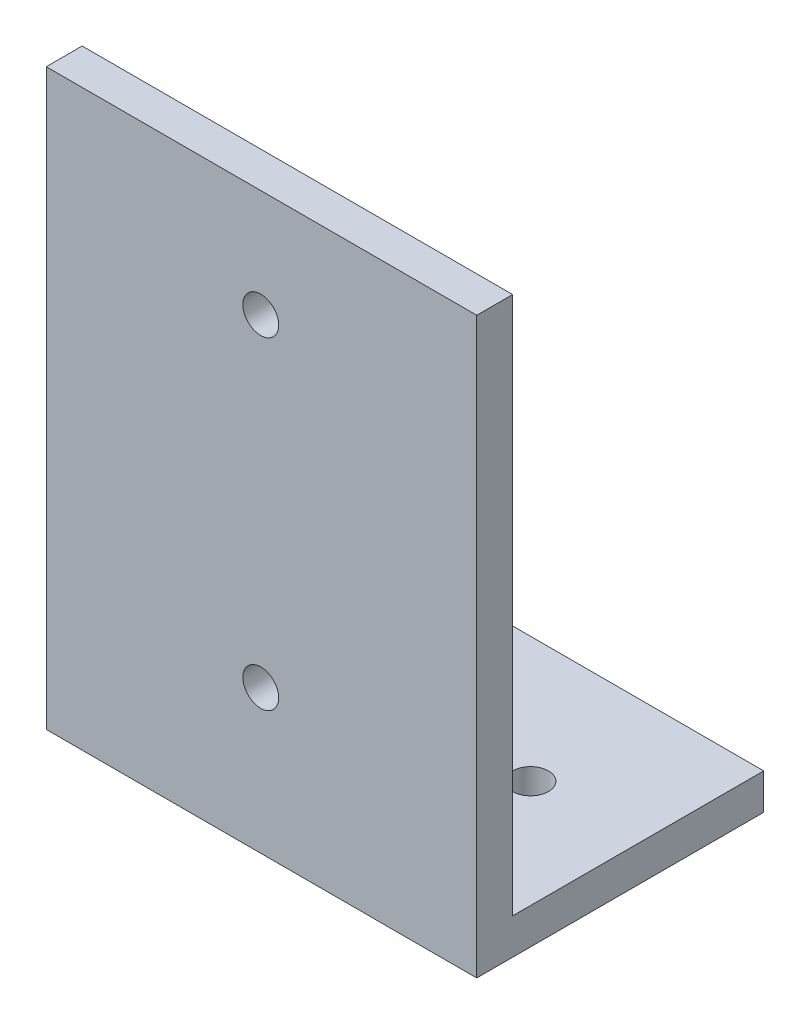
SolidWorks part; units mm, degrees
ref_plane "Front" through (0, 0, 0) normal (0, 0, 1) x (1, 0, 0)
ref_plane "Top" through (0, 0, 0) normal (0, 1, 0) x (1, 0, 0)
ref_plane "Right" through (0, 0, 0) normal (1, 0, 0) x (0, 0, -1)
sketch "Sketch1" plane through (0, 0, 0) normal (1, 0, 0) x (0, 0, -1)
  line L0 (0, 0) -> (0, 50.8)
  line L1 (0, 0) -> (25.4, 0)
  line L2 (3.175, 3.175) -> (3.175, 50.8)
  line L3 (3.175, 3.175) -> (25.4, 3.175)
  line L4 (0, 50.8) -> (3.175, 50.8)
  line L5 (25.4, 0) -> (25.4, 3.175)
  dimension "D1" = 50.8
  dimension "D2" = 25.4
  dimension "D3" = 3.175
extrude "Boss-Extrude1" add sketch "Sketch1" along normal blind 38.1
sketch "Sketch2" plane through (0, 3.175, 0) normal (0, 1, 0) x (1, 0, 0)
  line L0 (38.1, 14.2875) -> (28.575, 14.2875) construction
  line L1 (38.1, 25.4) -> (38.1, 3.175) construction
  line L2 (19.05, 3.175) -> (19.05, 25.4) construction
  line L3 (38.1, 3.175) -> (0, 3.175) construction
  line L4 (38.1, 25.4) -> (0, 25.4) construction
  circle A0 centre (28.575, 14.2875) radius 1.5875
  circle A1 centre (9.525, 14.2875) radius 1.5875
  dimension "D2" = 3.175
  dimension "D1" = 9.525
extrude "Cut-Extrude1" cut sketch "Sketch2" against normal up to next
sketch "Sketch3" plane through (0, 0, -3.175) normal (0, 0, -1) x (-1, 0, 0)
  line L0 (-18.9833, 3.175) -> (-18.9833, 12.7) construction
  line L1 (-38.1, 3.175) -> (0, 3.175) construction
  line L2 (-38.1, 26.9875) -> (0, 26.9875) construction
  line L3 (-38.1, 3.175) -> (-38.1, 50.8) construction
  line L4 (0, 3.175) -> (0, 50.8) construction
  circle A0 centre (-18.9833, 12.7) radius 1.5875
  circle A1 centre (-18.9833, 41.275) radius 1.5875
  dimension "D2" = 3.175
  dimension "D1" = 9.525
extrude "Cut-Extrude2" cut sketch "Sketch3" against normal up to next
